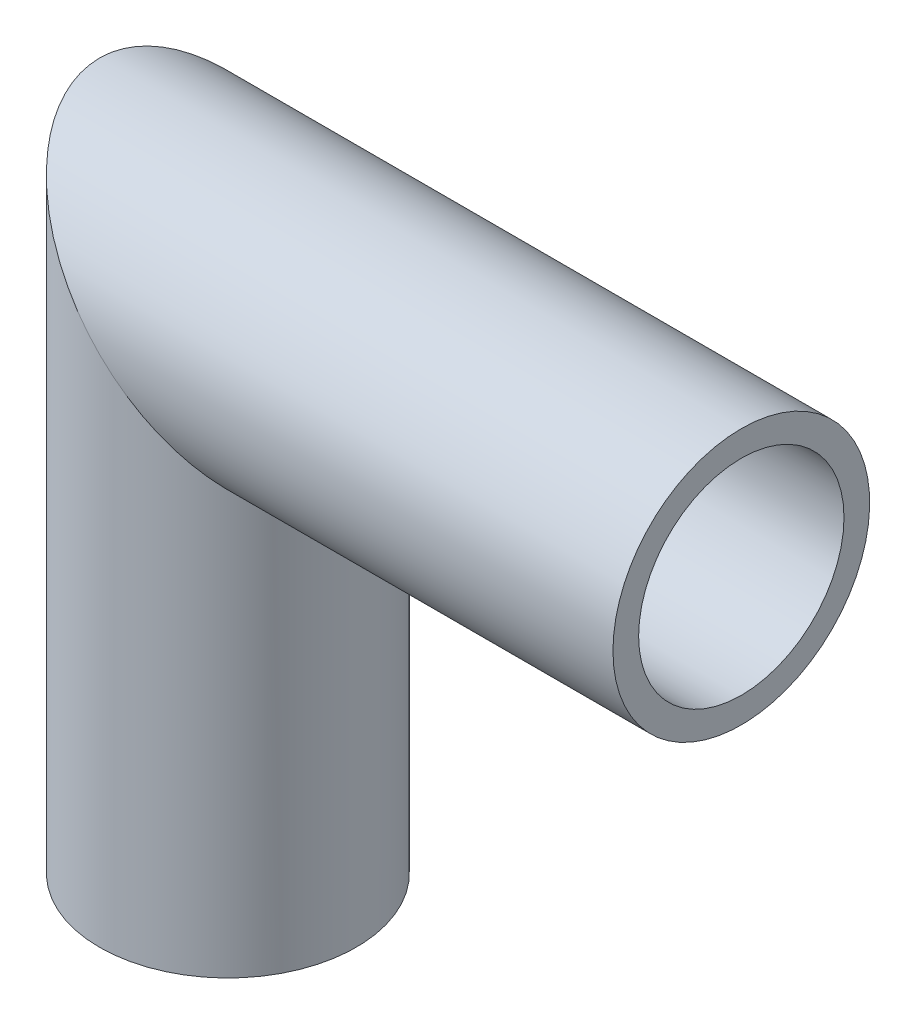
SolidWorks part; units mm, degrees
material "ABS"
ref_plane "前视基准面" through (0, 0, 0) normal (0, 0, 1) x (1, 0, 0)
ref_plane "上视基准面" through (0, 0, 0) normal (0, 1, 0) x (1, 0, 0)
ref_plane "右视基准面" through (0, 0, 0) normal (1, 0, 0) x (0, 0, -1)
sketch "草图1" plane through (0, 0, 0) normal (0, 1, 0) x (1, 0, 0)
  circle A0 centre (0, 0) radius 10
  circle A1 centre (0, 0) radius 12.5
sketch "草图2" plane through (0, 0, 0) normal (0, 0, 1) x (1, 0, 0)
  line L0 (0, 0) -> (0, 50)
  line L1 (0, 50) -> (50, 50)
sweep "扫描1" add profiles "草图1" path "草图2"
ref_plane "基准面1" through (0, 37.5, 0) normal (0, -1, 0) x (-1, 0, 0)
ref_plane "基准面2" through (12.5, 0, 0) normal (1, 0, 0) x (0, 0, -1)
